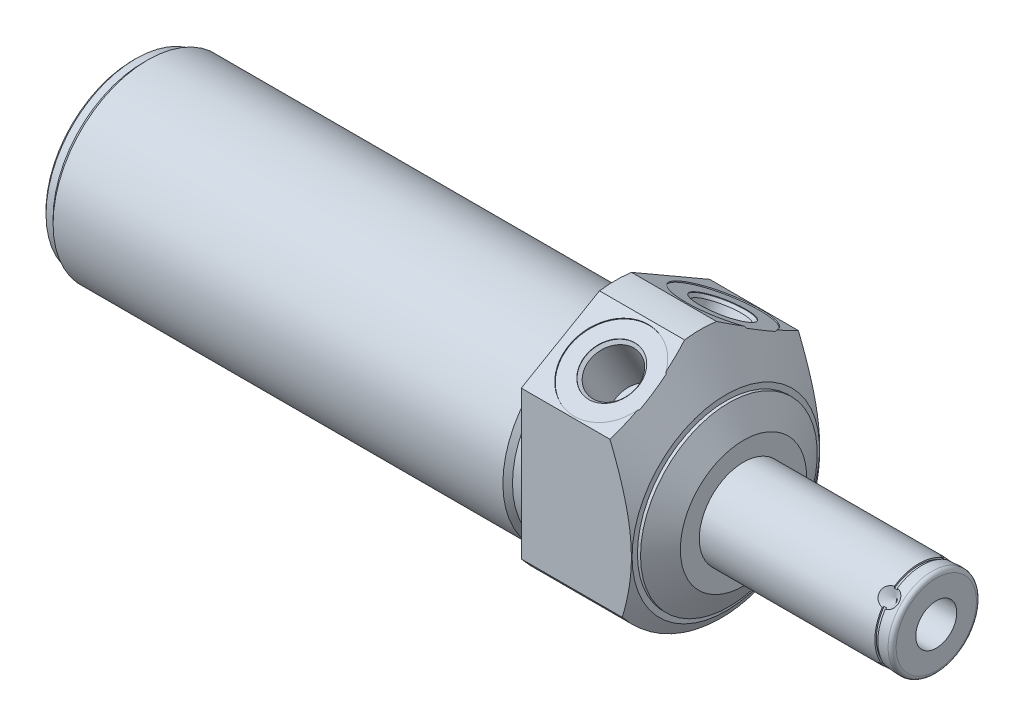
SolidWorks part; units mm, degrees
material "Alloy Steel"
ref_plane "Front Plane" through (0, 0, 0) normal (0, 0, 1) x (1, 0, 0)
ref_plane "Top Plane" through (0, 0, 0) normal (0, 1, 0) x (1, 0, 0)
ref_plane "Right Plane" through (0, 0, 0) normal (1, 0, 0) x (0, 0, -1)
sketch "Sketch1" plane through (0, 0, 0) normal (1, 0, 0) x (0, 0, -1)
  circle A0 centre (0, 0) radius 37.5
  dimension "D1" = 75
extrude "Extrude1" add sketch "Sketch1" along normal blind 32.1818 and the other way blind 121.3612
sketch "Sketch2" plane through (0, 0, 0) normal (1, 0, 0) x (0, 0, -1)
  line L0 (-14.6964, -4.445) -> (14.6964, -4.445) construction
  circle A0 centre (0, -4.445) radius 23.8125
  circle A1 centre (0, 0) radius 37.5 construction
  circle A2 centre (0, 0) radius 37.5
  dimension "D1" = 47.625
  dimension "D2" = 4.445
extrude "Cut-Extrude1" cut sketch "Sketch2" against normal up to next
sketch "Sketch4" plane through (32.1818, 0, 0) normal (-1, 0, 0) x (0, 0, 1)
  line L0 (23.6855, -18.6755) -> (23.6855, 18.5419)
  line L1 (23.6855, 18.5419) -> (4.0254, 29.8927)
  line L2 (-23.6855, -18.6755) -> (-23.6855, 18.5419)
  line L3 (-23.6855, 18.5419) -> (-4.0254, 29.8927)
  line L4 (0, -20.9029) -> (0, 19.86) construction
  circle A0 centre (0, 0) radius 37.5 construction
  circle A1 centre (0, 0) radius 37.5
  arc A7 (4.0254, 29.8927) -> (-4.0254, 29.8927) centre (0, 0) ccw
  arc A8 (-23.6855, -18.6755) -> (23.6855, -18.6755) centre (0, 0) ccw
  dimension "D4" = 60.325
  dimension "D1" = 47.371
  dimension "D2" = 60
  dimension "D3" = 31.75
extrude "Cut-Extrude3" cut sketch "Sketch4" along normal up to surface (32.1818 mm away) up to face at (0, -4.445, -23.8125)
sketch "Sketch6" plane through (0, 0, 0) normal (0, 0, 1) x (1, 0, 0)
  line L0 (19.6966, 33.055) -> (27.7368, 19.129)
  line L1 (1.9872, -4.445) -> (19.8625, -4.445) construction
  line L2 (-121.3612, -4.445) -> (0, -4.445) construction
  line L4 (32.1818, 11.43) -> (32.1818, 33.055)
  line L5 (32.1818, 33.055) -> (19.6966, 33.055)
  line L7 (27.7368, 19.129) -> (27.7368, 17.78)
  line L8 (27.7368, 17.78) -> (28.5156, 17.78)
  line L9 (28.5156, 17.78) -> (32.1818, 11.43)
  line L11 (32.1818, -18.6755) -> (32.1818, 18.5419) construction
  dimension "D1" = 31.75
  dimension "D2" = 75
  dimension "D3" = 44.45
  dimension "D4" = 4.445
  dimension "D5" = 30
revolve "Cut-Revolve2" cut sketch "Sketch6" angle 360 about L1
ref_plane "Plane17" through (13.0048, 0, 0) normal (-1, 0, 0) x (0, 0, 1)
sketch "S2D0002" plane through (13.0048, 13.7124, 8.6091) normal (1, 0, 0) x (0, 0.4226, -0.9063)
  line L0 (6.0881, 12.0431) -> (10.1619, 12.3995)
  line L1 (6.0881, 12.0431) -> (6.0992, 11.9166)
  line L2 (6.0992, 11.9166) -> (5.4527, 11.1461)
  line L3 (5.4527, 11.1461) -> (6.6149, -2.1381)
  line L4 (6.6149, -2.1381) -> (0.6939, -2.6561)
  line L5 (0.6939, -2.6561) -> (-0.5635, 11.7162)
  line L6 (1.553, -12.4753) -> (0.3886, 0.834) construction
  line L7 (10.1398, 12.6526) -> (10.1619, 12.3995)
  line L8 (10.9923, 12.7272) -> (-11.6229, 10.7486) construction
  line L9 (10.1398, 12.6526) -> (-0.5635, 11.7162)
  dimension "D1" = 21.4884
  dimension "D2" = 0.254
  dimension "D3" = 0.127
  dimension "D4" = 13.3096
  dimension "D5" = 45
  dimension "D6" = 11.8872
  dimension "D7" = 14.1732
  dimension "D8" = 2.0828
revolve "Cut-Revolve3" cut sketch "S2D0002" angle 360 about L6
mirror "Mirror1" about plane through (0, 0, 0) normal (0, 0, 1) of "Cut-Revolve3"
sketch "Sketch10" plane through (0, 0, 0) normal (0, 0, 1) x (1, 0, 0)
  line L0 (0, 19.3675) -> (0, 18.161)
  line L1 (0, 18.161) -> (-3.302, 18.161)
  line L2 (-3.302, 18.161) -> (-4.5085, 19.3675)
  line L3 (-5.094, -4.445) -> (0.2426, -4.445) construction
  line L4 (0, 19.3675) -> (-4.5085, 19.3675)
  line L5 (-121.3612, -4.445) -> (0, -4.445) construction
  line L7 (0, 18.5419) -> (0, -1.9889) construction
  line L8 (0, 19.3675) -> (-121.3612, 19.3675) construction
  dimension "D1" = 45.212
  dimension "D2" = 3.302
  dimension "D3" = 45
revolve "Cut-Revolve6" cut sketch "Sketch10" angle 360 about L3
sketch "Sketch12" plane through (0, 0, 0) normal (0, 0, 1) x (1, 0, 0)
  line L0 (-121.3612, 19.3675) -> (-121.3612, 18.161)
  line L1 (-121.3612, 18.161) -> (-118.8212, 18.161)
  line L2 (-118.8212, 18.161) -> (-117.6147, 19.3675)
  line L3 (-50.9283, -4.445) -> (-48.1063, -4.445) construction
  line L4 (-121.3612, 19.3675) -> (-117.6147, 19.3675)
  line L5 (-121.3612, -4.445) -> (-4.5085, -4.445) construction
  line L6 (-4.5085, 19.3675) -> (-121.3612, 19.3675) construction
  line L7 (-121.3612, 19.3675) -> (-121.3612, -28.2575) construction
  dimension "D1" = 45.212
  dimension "D2" = 2.54
  dimension "D3" = 45
revolve "Cut-Revolve8" cut sketch "Sketch12" angle 360 about L3
chamfer "Chamfer1" distance 0.762 angle 45 1 edges at (-121.3612, -4.445, 22.606)
sketch "Sketch13" plane through (0, 0, 0) normal (0, 0, 1) x (1, 0, 0)
  line L0 (32.1818, -4.445) -> (80.658, -4.445)
  line L1 (80.658, -4.445) -> (80.658, -14.5415)
  line L2 (79.642, -15.5575) -> (32.1818, -15.5575)
  line L3 (32.1818, -15.5575) -> (32.1818, -4.445)
  line L4 (4.7498, -4.445) -> (27.0459, -4.445) construction
  line L5 (-117.6147, -4.445) -> (-4.5085, -4.445) construction
  line L6 (32.1818, -20.32) -> (32.1818, 11.43) construction
  line L7 (0, 18.5419) -> (0, -18.6755) construction
  arc A0 (79.642, -15.5575) -> (80.658, -14.5415) centre (79.642, -14.5415) ccw
  dimension "D2" = 1.016
  dimension "D1" = 80.658
  dimension "D3" = 22.225
revolve "Revolve1" add sketch "Sketch13" angle 360 about L4
ref_plane "Plane18" through (0, -2.2225, -2.2225) normal (0, 0.7071, 0.7071) x (-1, 0, 0)
sketch "S2D0001" plane through (0, 0, 0) normal (0, 0, 1) x (1, 0, 0)
  line L0 (80.658, 0.7112) -> (63.64, 0.7112)
  line L1 (63.64, 0.7112) -> (60.5418, -4.445)
  line L2 (80.658, 0.7112) -> (80.658, -4.445)
  line L3 (80.658, -4.445) -> (60.5418, -4.445)
  line L4 (-2.8067, -4.445) -> (-15.8378, -4.445) construction
  line L5 (79.642, -4.445) -> (32.1818, -4.445) construction
  line L6 (80.658, -14.5415) -> (80.658, 5.6515) construction
  dimension "D1" = 10.3124
  dimension "D2" = 17.018
  dimension "D3" = 59
revolve "Cut-Revolve9" cut sketch "S2D0001" angle 360 about L4
sketch "Sketch16" plane through (0, -7.5881, 3.1431) normal (0, -0.7071, -0.7071) x (1, 0, 0)
  line L0 (76.6956, -15.5575) -> (74.2826, -15.5575)
  line L1 (74.2826, -15.5575) -> (76.6956, -13.1445)
  line L2 (76.6956, -15.5575) -> (76.6956, -13.1445)
  line L3 (76.6956, -3.4788) -> (76.6956, 0.0794) construction
  line L4 (80.658, -14.5415) -> (80.658, 5.6515) construction
  line L5 (32.1818, -15.5575) -> (79.642, -15.5575) construction
  dimension "D1" = 3.9624
  dimension "D2" = 4.826
  dimension "D3" = 45
revolve "Cut-Revolve10" cut sketch "Sketch16" angle 360 about L3
pattern_circular "CirPattern1" count 4 over 360 about axis through (4.7498, -4.445, 0) along (-1, 0, 0) of "Cut-Revolve10"
sketch "Sketch21" plane through (0, 0, 0) normal (0, 0, 1) x (1, 0, 0)
  line L1 (76.3146, 6.6675) -> (77.0766, 6.6675)
  line L2 (76.3146, 6.6675) -> (76.3146, 6.2865)
  line L3 (76.3146, 6.2865) -> (77.0766, 6.2865)
  line L4 (77.0766, 6.6675) -> (77.0766, 6.2865)
  line L5 (76.6956, -0.7782) -> (76.6956, 2.3032) construction
  line L7 (23.8735, -4.445) -> (50.6625, -4.445) construction
  line L10 (80.658, -14.5415) -> (80.658, 5.6515) construction
  line L11 (85.9315, -4.445) -> (67.0631, -4.445) construction
  dimension "D1" = 0.381
  dimension "D2" = 0.762
  dimension "D3" = 3.5814
  dimension "D4" = 11.1125
revolve "Cut-Revolve11" cut sketch "Sketch21" angle 360 about L7
